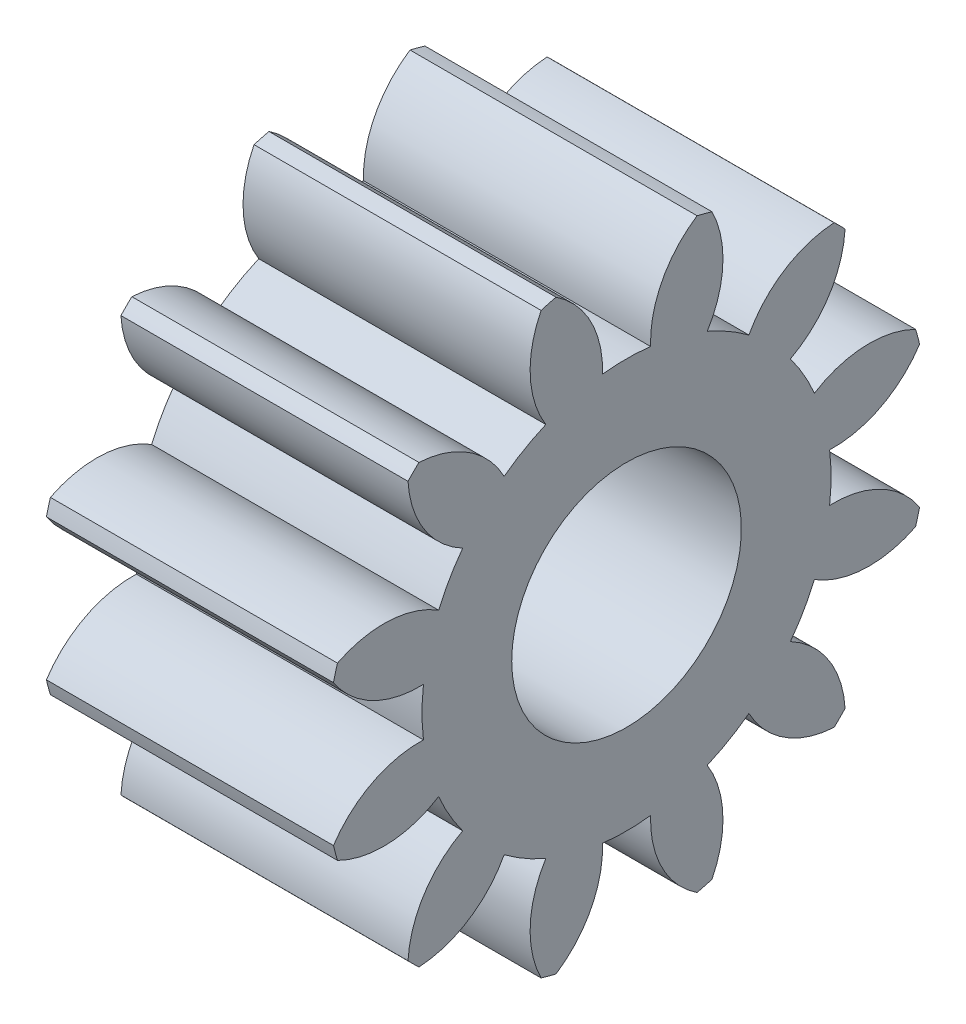
SolidWorks part; units mm, degrees
ref_plane "Plane1" through (0, 0, 0) normal (0, 0, 1) x (1, 0, 0)
ref_plane "Plane2" through (0, 0, 0) normal (0, 1, 0) x (1, 0, 0)
ref_plane "Plane3" through (0, 0, 0) normal (1, 0, 0) x (0, 0, -1)
other "Configuration Table"
sketch "HoldingSke" plane through (0, 0, 0) normal (0, 1, 0) x (1, 0, 0)
  line L0 (0, 0) -> (0.6521, -0.1386)
  line L1 (-15, 0) -> (100, 0) construction
  line L2 (0, 0) -> (-2.1039, 2.3779)
  line L3 (0, 0) -> (-11.863, 4.5341)
  line L4 (0, 0) -> (8.4473, 1.7955)
  line L5 (0, 0) -> (-46.8476, -17.4728)
  line L6 (0, 0) -> (-8.2896, -5.593)
  line L7 (-2.1039, 2.3779) -> (8.6586, 51.2059)
  line L8 (-76.2, 54.61) -> (-74.8, 54.61)
  line L9 (-71.009, 38.7566) -> (-53.1078, 45.2721)
  line L10 (-76.2, 71.12) -> (104.1128, 71.12)
  line L11 (0, 0) -> (-10, 0)
  line L12 (-76.2, 101.6) -> (-76.147, 101.6)
  line L13 (24.9733, 27.94) -> (52.9518, 28.4284)
  line L14 (24.9733, 27.94) -> (24.9743, 27.94)
  line L15 (24.9733, 27.94) -> (100.4006, 29.5858)
  line L16 (-63.627, -1.5) -> (-12.827, -1.5)
  circle A0 centre (0, 0) radius 4
  circle A1 centre (0, 0) radius 7.124
  circle A2 centre (0, 0) radius 37.5
  circle A3 centre (0, 0) radius 4
  dimension "MHD" = 14.248
  dimension "Hub_dia" = 75
  dimension "Bore" = 8
  dimension "MBD" = 8
  dimension "Num_teeth" = 12
  dimension "Pitch" = 0.6667
  dimension "Overall_len" = 50
  dimension "Show_teeth" = 12
  dimension "Thickness" = 10
  dimension "OAL" = 50.0001
  dimension "T_dim" = 1.4
  dimension "Ap" = 20
  dimension "H" = 19.05
  dimension "Pitch_radius" = 180.3128
  dimension "Width" = 10
  dimension "Backlash" = 0.053
  dimension "Addendum_fac" = 1
  dimension "Dedendum_fac" = 1.25
  dimension "Clearance_fac" = 0.25
  dimension "Dedendum_add" = 0.001
  dimension "Module" = 1.5
sketch "BasProSke" plane through (0, 0, 0) normal (0, 1, 0) x (1, 0, 0)
  line L0 (-10, 0) -> (60, 0) construction
  line L1 (0, 0) -> (0, 10.5)
  line L2 (0, 0) -> (10, 0)
  line L3 (10, 0) -> (10, 10.5)
  line L4 (10, 10.5) -> (0, 10.5)
  dimension "Thickness" = 10
  dimension "Diameter" = 21
revolve "Base-Revolve" add sketch "BasProSke" angle 360 about L0
sketch "TooCutSke" plane through (0, 0, 0) normal (1, 0, 0) x (0, 0, -1)
  line L1 (0, 0) -> (0, 107) construction
  line L2 (0, 0) -> (-1.2674, 8.9103) construction
  line L3 (0, 0) -> (-4.625, 17.2606) construction
  line L4 (-1.2674, 8.9103) -> (-2.3125, 8.6303) construction
  arc A0 (0.8378, 7.0746) -> (-0.8378, 7.0746) centre (0, 0) ccw
  arc A1 (2.4865, 10.2275) -> (-2.4865, 10.2275) centre (0, 0) ccw
  circle A2 centre (0, 0) radius 9 construction
  circle A3 centre (0, 0) radius 8.4572 construction
  arc A4 (-0.8378, 7.0746) -> (-2.4865, 10.2275) centre (-4.4355, 7.2007) ccw
  arc A5 (2.4865, 10.2275) -> (0.8378, 7.0746) centre (4.4355, 7.2007) ccw
  dimension "Root_dia" = 14.248
  dimension "Overcut_dia" = 21.0508
  dimension "Pitch_dia" = 18
  dimension "Base_dia" = 16.9145
  dimension "Flank_rad" = 3.6
  dimension "Half_ang" = 15
  dimension "Half_CT" = 1.082
extrude "ToothCut" cut sketch "TooCutSke" along normal through all
fillet "Breaks" [suppressed] radius 0.03
fillet "RootFillets" [suppressed] radius 0.376
pattern_circular "TeethCuts" count 12 every 30 about axis through (-10, 0, 0) along (1, 0, 0) of "ToothCut", "RootFillets", "Breaks"
sketch "HubNeaOneSke" plane through (0, 0, 0) normal (-1, 0, 0) x (0, 0, 1)
  circle A0 centre (0, 0) radius 7.124
  dimension "Diameter" = 14.248
extrude "HubNearOne" [suppressed] add sketch "HubNeaOneSke" along normal blind 40.0001
sketch "HubNeaBotSke" plane through (0, 0, 0) normal (-1, 0, 0) x (0, 0, 1)
  circle A0 centre (0, 0) radius 7.124
  dimension "Diameter" = 14.248
extrude "HubNearBoth" [suppressed] add sketch "HubNeaBotSke" along normal blind 20
ref_plane "FarPln" through (10, 0, 0) normal (1, 0, 0) x (0, 0, -1)
sketch "HubFarSke" plane through (10, 0, 0) normal (1, 0, 0) x (0, 0, -1)
  circle A0 centre (0, 0) radius 7.124
  dimension "Diameter" = 14.248
extrude "HubFar" [suppressed] add sketch "HubFarSke" along normal blind 20
sketch "BorSke" plane through (0, 0, 0) normal (1, 0, 0) x (0, 0, -1)
  circle A0 centre (0, 0) radius 4
  dimension "Diameter" = 8
extrude "Bore" cut sketch "BorSke" along normal mid plane 100.0001
sketch "KeySke" plane through (0, 0, 0) normal (1, 0, 0) x (0, 0, -1)
  line L0 (-1.5, 0) -> (-1.5, 5.4)
  line L1 (-1.5, 5.4) -> (1.5, 5.4)
  line L2 (1.5, 5.4) -> (1.5, 0)
  line L3 (0, 0) -> (0, 34) construction
  line L4 (-1.5, 0) -> (1.5, 0)
  dimension "Offset" = 5.4
  dimension "Width" = 3
extrude "Keyway" [suppressed] cut sketch "KeySke" along normal mid plane 100.0001
pattern_circular "Keyway2" [suppressed] count 2 every 90 about axis through (-10, 0, 0) along (1, 0, 0)
equation "' \"Module@HoldingSke\" = 6.35"
equation "' \"Num_teeth@HoldingSke\" = 12"
equation "' \"Ap@HoldingSke\" =  20"
equation "' \"Ap@HoldingSke\" = 20"
equation "' \"Width@HoldingSke\" = 0.5 * 25.4"
equation "' \"Hub_dia@HoldingSke\"= 1 * 25.4"
equation "' \"Hub_dia@HoldingSke\" = 1 * 25.4"
equation "' \"Overall_len@HoldingSke\" = 1.0 * 25.4"
equation "' \"Bore@HoldingSke\" = 0.75 * 25.4"
equation "' \"T_dim@HoldingSke\" = 0.1 * 25.4"
equation "' \"Width@KeySke\" = 0.25 * 25.4"
equation "' \"Show_teeth@HoldingSke\" = 13"
equation "' \"Backlash@HoldingSke\" = 0.009 * 25.4"
equation "' \"Addendum_fac@HoldingSke\" = 1.0"
equation "' \"Dedendum_fac@HoldingSke\" = 1.25"
equation "' \"Dedendum_add@HoldingSke\" = 0.00005 * 25.4"
equation "' \"Clearance_fac@HoldingSke\" = 0.25"
equation "\"Pitch@HoldingSke\" = 1 / \"Module@HoldingSke\""
equation "\"Overcut_dia@TooCutSke\" = (\"Num_teeth@HoldingSke\" + 2 * \"Addendum_fac@HoldingSke\") / \"Pitch@HoldingSke\" + 0.002 * 25.4"
equation "\"Pitch_dia@TooCutSke\" = \"Num_teeth@HoldingSke\" / \"Pitch@HoldingSke\""
equation "\"Base_dia@TooCutSke\" = \"Num_teeth@HoldingSke\" / \"Pitch@HoldingSke\" * cos((\"Ap@HoldingSke\"  * 3.14159265 / 180))"
equation "\"Root_dia@TooCutSke\" = (\"Num_teeth@HoldingSke\" + 2) / \"Pitch@HoldingSke\" - 2 * (\"Addendum_fac@HoldingSke\" + \"Dedendum_fac@HoldingSke\") / \"Pitch@HoldingSke\" - \"Dedendum_add@HoldingSke\" * 2"
equation "\"Half_ang@TooCutSke\" = 180 / \"Num_teeth@HoldingSke\""
equation "\"Half_CT@TooCutSke\" = \"Num_teeth@HoldingSke\" / \"Pitch@HoldingSke\" * sin((3.14159265 / 2 / \"Num_teeth@HoldingSke\")) / 2 - 7 * \"Backlash@HoldingSke\" / 4"
equation "\"Flank_rad@TooCutSke\" = \"Num_teeth@HoldingSke\" / \"Pitch@HoldingSke\" / 5"
equation "\"Radius@RootFillets\" = \"Clearance_fac@HoldingSke\" / \"Pitch@HoldingSke\" + \"Dedendum_add@HoldingSke\""
equation "\"Break_rad@Breaks\" = 0.02 / \"Pitch@HoldingSke\""
equation "\"Thickness@HoldingSke\" = \"Width@HoldingSke\""
equation "\"OAL@HoldingSke\" = \"Thickness@HoldingSke\""
equation "\"MHD@HoldingSke\" = (\"Num_teeth@HoldingSke\" + 2) / \"Pitch@HoldingSke\" - 2 * (\"Addendum_fac@HoldingSke\" + \"Dedendum_fac@HoldingSke\")  / \"Pitch@HoldingSke\" - \"Dedendum_add@HoldingSke\" * 2"
equation "\"MBD@HoldingSke\" = (\"Num_teeth@HoldingSke\" + 2) / \"Pitch@HoldingSke\" - 2 * (\"Addendum_fac@HoldingSke\" + \"Dedendum_fac@HoldingSke\")  / \"Pitch@HoldingSke\" - \"Dedendum_add@HoldingSke\" * 2 - 0.002 * 25.4"
equation "\"MHD@HoldingSke\" = ((sgn( \"MHD@HoldingSke\" - \"Hub_dia@HoldingSke\" )-1)*( \"MHD@HoldingSke\" - \"Hub_dia@HoldingSke\" ))/-2+ \"Hub_dia@HoldingSke\""
equation "\"MBD@HoldingSke\" = ((sgn( \"MBD@HoldingSke\" - \"Bore@HoldingSke\" )-1)*( \"MBD@HoldingSke\" - \"Bore@HoldingSke\" ))/-2+ \"Bore@HoldingSke\""
equation "\"OAL@HoldingSke\" = ((sgn( \"OAL@HoldingSke\" - \"Overall_len@HoldingSke\" )+1)*( \"OAL@HoldingSke\" - \"Overall_len@HoldingSke\" ))/2 + \"Overall_len@HoldingSke\" + 0.000002 * 25.4"
equation "\"Num_teeth@TeethCuts\" = int( \"Show_teeth@HoldingSke\" ) + 1"
equation "\"Num_teeth@TeethCuts\" = ((sgn( \"Num_teeth@TeethCuts\" - \"Num_teeth@HoldingSke\" )-1)*( \"Num_teeth@TeethCuts\" - \"Num_teeth@HoldingSke\" ))/-2+ \"Num_teeth@HoldingSke\""
equation "\"Num_teeth@TeethCuts\" = ((sgn( \"Num_teeth@TeethCuts\" - 2.0)+1)*( \"Num_teeth@TeethCuts\" - 2.0))/2 +2.0"
equation "\"Angle@TeethCuts\" = 360.0 / \"Num_teeth@HoldingSke\""
equation "\"Diameter@BasProSke\" = (\"Num_teeth@HoldingSke\" + 2 * \"Addendum_fac@HoldingSke\") / \"Pitch@HoldingSke\""
equation "\"Thickness@BasProSke\"  = \"Thickness@HoldingSke\""
equation "' \"Fillet_rad@BasProSke\" =  \"Thickness@HoldingSke\" * 0.05"
equation "' \"Fillet_rad@BasProSke\" = \"Thickness@HoldingSke\" * 0.05"
equation "\"MHD@HoldingSke\" = ((sgn( \"MHD@HoldingSke\" - \"Root_dia@TooCutSke\" )-1)*( \"MHD@HoldingSke\" - \"Root_dia@TooCutSke\" ))/-2+ \"Root_dia@TooCutSke\""
equation "\"Diameter@HubNeaOneSke\" = \"MHD@HoldingSke\""
equation "\"Length@HubNearOne\" = \"OAL@HoldingSke\" - \"Thickness@BasProSke\""
equation "\"Diameter@HubNeaBotSke\" = \"MHD@HoldingSke\""
equation "\"Length@HubNearBoth\" = ( \"OAL@HoldingSke\" - \"Thickness@BasProSke\" ) / 2.0"
equation "\"Thickness@FarPln\" = \"Thickness@BasProSke\""
equation "\"Diameter@HubFarSke\" = \"MHD@HoldingSke\""
equation "\"Length@HubFar\" = ( \"OAL@HoldingSke\" - \"Thickness@BasProSke\" ) / 2.0"
equation "\"Diameter@BorSke\" = \"MBD@HoldingSke\""
equation "\"D1@Bore\" = \"OAL@HoldingSke\" * 2.0"
equation "\"D1@Keyway\" = \"OAL@HoldingSke\" * 2.0"
equation "\"Offset@KeySke\" = \"T_dim@HoldingSke\" + \"MBD@HoldingSke\" / 2.0"
